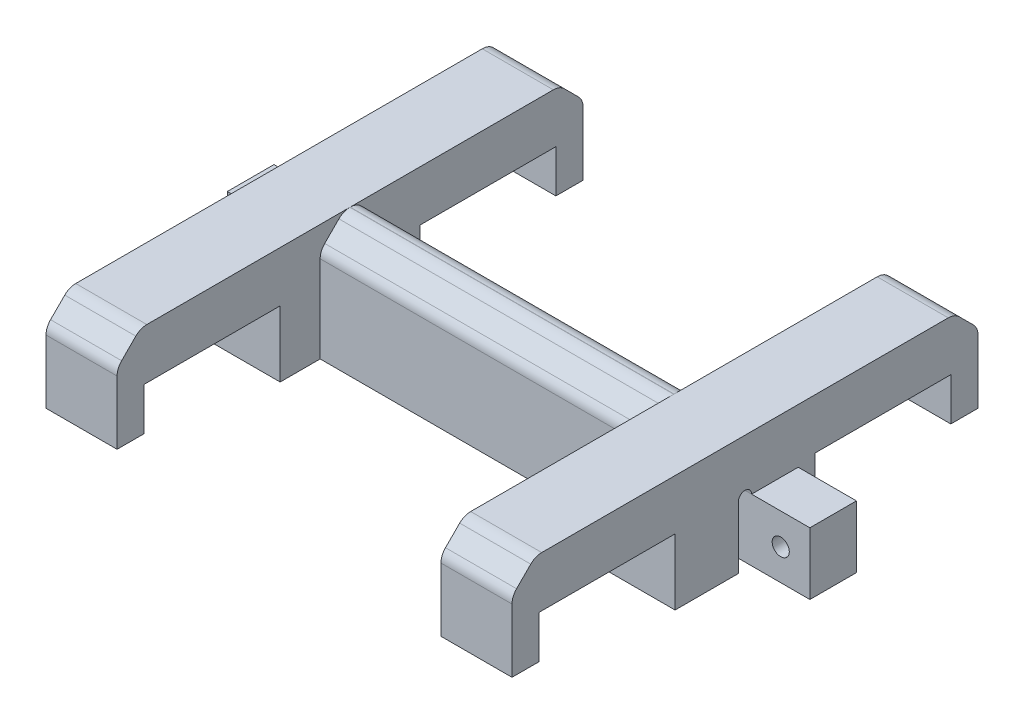
SolidWorks part; units mm, degrees
material "ABS"
ref_plane "Front Plane" through (0, 0, 0) normal (0, 0, 1) x (1, 0, 0)
ref_plane "Top Plane" through (0, 0, 0) normal (0, 1, 0) x (1, 0, 0)
ref_plane "Right Plane" through (0, 0, 0) normal (1, 0, 0) x (0, 0, -1)
sketch "Sketch1" plane through (0, 0, 0) normal (0, 0, 1) x (1, 0, 0)
  line L1 (30, -7.5) -> (-30, -7.5)
  line L2 (30, -7.5) -> (30, 7.5)
  line L3 (30, 7.5) -> (-30, 7.5)
  line L4 (-30, -7.5) -> (-30, 7.5)
  line L5 (30, -7.5) -> (-30, 7.5) construction
  line L6 (30, 7.5) -> (-30, -7.5) construction
  point P0 (0, 0)
  dimension "D1" = 60
  dimension "D2" = 15
extrude "Boss-Extrude1" add sketch "Sketch1" along normal mid plane 60
sketch "Sketch2" plane through (0, -7.5, 0) normal (0, -1, 0) x (1, 0, 0)
  line L0 (-30, 30) -> (-30, -30) construction
  line L1 (30, -0.85) -> (-30, -0.85)
  line L2 (30, -0.85) -> (30, 0.85)
  line L3 (30, 0.85) -> (-30, 0.85)
  line L4 (-30, -0.85) -> (-30, 0.85)
  line L5 (30, -0.85) -> (-30, 0.85) construction
  line L6 (30, 0.85) -> (-30, -0.85) construction
  point P0 (0, 0)
  dimension "D1" = 1.7
extrude "Cut-Extrude1" cut sketch "Sketch2" against normal blind 8
sketch "Sketch3" plane through (0, -7.5, 0) normal (0, -1, 0) x (1, 0, 0)
  line L0 (-30, -0.85) -> (-30, -30) construction
  line L1 (30, -13) -> (-30, -13)
  line L2 (30, -13) -> (30, -11.2)
  line L3 (30, -11.2) -> (-30, -11.2)
  line L4 (-30, -13) -> (-30, -11.2)
  line L5 (30, -13) -> (-30, -11.2) construction
  line L6 (30, -11.2) -> (-30, -13) construction
  line L7 (30, -0.85) -> (30, -30) construction
  line L9 (30, -24.3) -> (-30, -24.3)
  line L10 (30, -24.3) -> (30, -22.5)
  line L11 (30, -22.5) -> (-30, -22.5)
  line L12 (-30, -24.3) -> (-30, -22.5)
  line L13 (30, -24.3) -> (-30, -22.5) construction
  line L14 (30, -22.5) -> (-30, -24.3) construction
  point P0 (0, -12.1)
  point P5 (0, -23.4)
  dimension "D1" = 11.2
  dimension "D2" = 1.8
  dimension "D3" = 22.5
extrude "Cut-Extrude2" cut sketch "Sketch3" against normal blind 8.5
sketch "Sketch4" plane through (0, -7.5, 0) normal (0, -1, 0) x (1, 0, 0)
  line L0 (-30, 30) -> (-30, 0.85) construction
  line L1 (30, 6) -> (-30, 6)
  line L2 (30, 6) -> (30, 30)
  line L3 (30, 30) -> (-30, 30)
  line L4 (-30, 6) -> (-30, 30)
  line L5 (30, 6) -> (-30, 30) construction
  line L6 (30, 30) -> (-30, 6) construction
  line L7 (30, 30) -> (30, 0.85) construction
  point P0 (0, 18)
  dimension "D1" = 24
extrude "Cut-Extrude3" cut sketch "Sketch4" against normal blind 3
sketch "Sketch5" plane through (0, -7.5, 0) normal (0, -1, 0) x (1, 0, 0)
  line L0 (30, 30) -> (-30, 30) construction
  line L1 (20.85, 6) -> (-20.85, 6)
  line L2 (20.85, 6) -> (20.85, 30)
  line L3 (20.85, 30) -> (-20.85, 30)
  line L4 (-20.85, 6) -> (-20.85, 30)
  line L5 (20.85, 6) -> (-20.85, 30) construction
  line L6 (20.85, 30) -> (-20.85, 6) construction
  line L7 (-30, 6) -> (30, 6) construction
  point P0 (0, 18)
  dimension "D1" = 41.7
extrude "Cut-Extrude4" cut sketch "Sketch5" against normal blind 27
sketch "Sketch6" plane through (0, -7.5, 0) normal (0, -1, 0) x (1, 0, 0)
  line L0 (-30, -13) -> (-30, -22.5) construction
  line L1 (30, -22.5) -> (-30, -22.5)
  line L2 (30, -22.5) -> (30, -13)
  line L3 (30, -13) -> (-30, -13)
  line L4 (-30, -22.5) -> (-30, -13)
  line L5 (30, -22.5) -> (-30, -13) construction
  line L6 (30, -13) -> (-30, -22.5) construction
  line L7 (30, -24.3) -> (30, -22.5) construction
  line L8 (30, -22.5) -> (-30, -22.5) construction
  point P0 (0, -17.75)
extrude "Cut-Extrude5" cut sketch "Sketch6" against normal up to surface (8.5 mm away) up to face at (0, 1, -12.1)
sketch "Sketch7" plane through (0, 1, 0) normal (0, -1, 0) x (1, 0, 0)
  line L0 (0, -11.2) -> (0, -24.3) construction
  line L1 (30, -26.5) -> (-30, -26.5)
  line L2 (30, -26.5) -> (30, -9)
  line L3 (30, -9) -> (-30, -9)
  line L4 (-30, -26.5) -> (-30, -9)
  line L5 (30, -26.5) -> (-30, -9) construction
  line L6 (30, -9) -> (-30, -26.5) construction
  line L7 (30, -11.2) -> (-30, -11.2) construction
  line L8 (-30, -24.3) -> (30, -24.3) construction
  line L9 (-30, -0.85) -> (-30, -11.2) construction
  point P0 (0, -17.75)
  dimension "D1" = 17.5
extrude "Cut-Extrude6" cut sketch "Sketch7" along normal blind 25
mirror "Mirror1" about plane through (0, 0, 0) normal (0, 0, 1) of "Cut-Extrude6", "Cut-Extrude4", "Cut-Extrude2", "Cut-Extrude3", "Cut-Extrude5"
sketch "Sketch9" plane through (0, -7.5, 0) normal (0, -1, 0) x (1, 0, 0)
  line L0 (0, 0) -> (-34.0408, 0) construction
  line L1 (-20.85, 6) -> (-30, 6)
  line L2 (-20.85, 6) -> (-20.85, 9)
  line L3 (-20.85, 9) -> (-30, 9)
  line L4 (-30, 6) -> (-30, 9)
  line L5 (-20.85, 6) -> (-30, 9) construction
  line L6 (-20.85, 9) -> (-30, 6) construction
  line L7 (-20.85, -9) -> (-30, -6) construction
  line L8 (-20.85, -6) -> (-30, -9) construction
  line L9 (-30, -6) -> (-30, -9)
  line L10 (-20.85, -9) -> (-30, -9)
  line L11 (-20.85, -6) -> (-20.85, -9)
  line L12 (-20.85, -6) -> (-30, -6)
  line L13 (0, 0) -> (0, -10.4142) construction
  line L14 (20.85, -6) -> (30, -9) construction
  line L15 (20.85, -9) -> (30, -6) construction
  line L16 (20.85, 9) -> (30, 6) construction
  line L17 (20.85, 6) -> (30, 9) construction
  line L18 (20.85, -6) -> (30, -6)
  line L19 (20.85, -6) -> (20.85, -9)
  line L20 (20.85, -9) -> (30, -9)
  line L21 (30, -6) -> (30, -9)
  line L22 (30, 6) -> (30, 9)
  line L23 (20.85, 9) -> (30, 9)
  line L24 (20.85, 6) -> (20.85, 9)
  line L25 (20.85, 6) -> (30, 6)
  point P0 (-25.425, 7.5)
  point P14 (-25.425, -7.5)
  point P24 (25.425, -7.5)
  point P25 (25.425, 7.5)
extrude "Boss-Extrude2" add sketch "Sketch9" against normal blind 5
sketch "Sketch10" plane through (0, -7.5, 0) normal (0, -1, 0) x (1, 0, 0)
  line L0 (30, 0.85) -> (-30, 0.85) construction
  line L1 (-20.85, 9) -> (20.85, 9)
  line L2 (-20.85, 9) -> (-20.85, 3.85)
  line L3 (-20.85, 3.85) -> (20.85, 3.85)
  line L4 (20.85, 9) -> (20.85, 3.85)
  dimension "D1" = 3
extrude "Cut-Extrude7" cut sketch "Sketch10" against normal blind 23
mirror "Mirror2" about plane through (0, 0, 0) normal (0, 0, 1) of "Cut-Extrude7"
chamfer "Chamfer1" distance 3 angle 45 6 edges at (-25.425, 7.5, -30) (25.425, 7.5, -30) (25.425, 7.5, 30) (-25.425, 7.5, 30) (0, 7.5, -3.85) (0, 7.5, 3.85)
fillet "Fillet1" radius 2 12 edges at (-25.425, 7.5, -27) (-25.425, 4.5, -30) (25.425, 4.5, -30) (25.425, 7.5, -27) (25.425, 4.5, 30) (25.425, 7.5, 27) (-25.425, 4.5, 30) (-25.425, 7.5, 27) (0, 4.5, -3.85) (0, 7.5, -0.85) (0, 7.5, 0.85) (0, 4.5, 3.85)
sketch "Sketch11" plane through (0, 0, -0.85) normal (0, 0, 1) x (1, 0, 0)
  line L0 (0, 0) -> (0, -13.0316) construction
  line L1 (-30, 0.5) -> (-37.5, 0.5)
  line L2 (-30, 0.5) -> (-30, -7.5)
  line L3 (-30, -7.5) -> (-37.5, -7.5)
  line L4 (-37.5, 0.5) -> (-37.5, -7.5)
  line L5 (37.5, 0.5) -> (37.5, -7.5)
  line L6 (30, -7.5) -> (37.5, -7.5)
  line L7 (30, 0.5) -> (30, -7.5)
  line L8 (30, 0.5) -> (37.5, 0.5)
  dimension "D1" = 75
extrude "Boss-Extrude3" add sketch "Sketch11" against normal blind 6
sketch "Sketch12" plane through (0, 0, -6.85) normal (0, 0, -1) x (-1, 0, 0)
  line L0 (37.5, 0.5) -> (30, -7.5) construction
  circle A0 centre (33.75, -3.5) radius 1.9
  dimension "D1" = 3.8
extrude "Cut-Extrude8" cut sketch "Sketch12" against normal blind 4
hole_wizard "M2 Clearance Hole1" positions "Sketch15" profile "Sketch14" hole size "M2" standard "DIN"
sketch "Sketch15" plane through (0, 0, -6.85) normal (0, 0, -1) x (-1, 0, 0)
  point P0 (33.75, -3.5)
sketch "Sketch14" plane through (-33.75, -3.5, -6.85) normal (1, 0, 0) x (0, 1, 0)
  line L0 (0, 0) -> (0, 10)
  line L1 (0, 10) -> (1.1, 10)
  line L2 (1.1, 10) -> (1.1, 0)
  line L5 (1.1, 0) -> (0, 0)
  line L10 (0, 10) -> (-1.1, 10) construction
  line L11 (0, -6.35) -> (0, 107.95) construction
  dimension "Hole Dia." = 2.2
  dimension "Hole Depth" = 10
  dimension "Drill Angle" = 180
mirror "Mirror3" about plane through (0, 0, 0) normal (1, 0, 0) of "M2 Clearance Hole1", "Cut-Extrude8"
sketch "Sketch16" plane through (-37.5, 0, 0) normal (-1, 0, 0) x (0, 0, 1)
  line L0 (0.85, 0.5) -> (-0.85, 0.5) construction
  line L1 (-0.85, 0.5) -> (-0.85, -7.5) construction
  circle A0 centre (0, 0.5) radius 0.85
extrude "Cut-Extrude9" cut sketch "Sketch16" against normal blind 81
